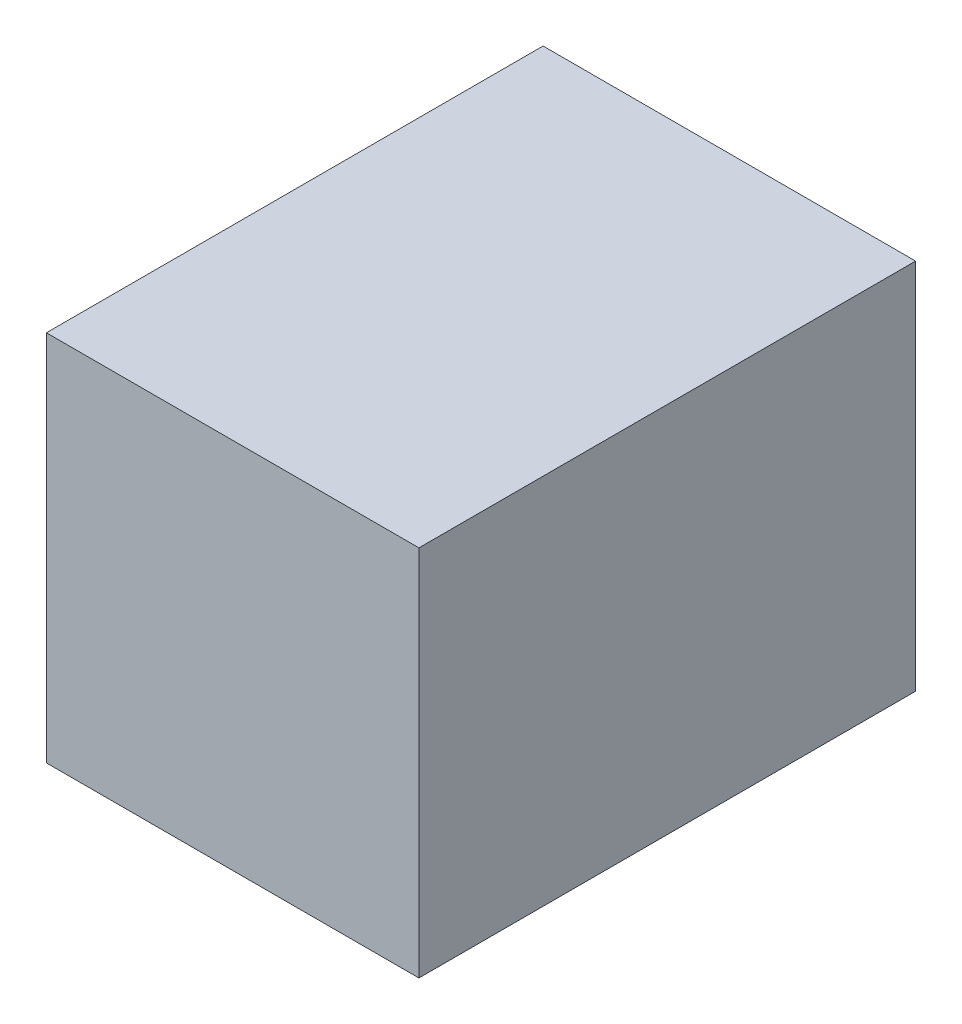
SolidWorks part; units mm, degrees
material "Plain Carbon Steel"
ref_plane "Front Plane" through (0, 0, 0) normal (0, 0, 1) x (1, 0, 0)
ref_plane "Top Plane" through (0, 0, 0) normal (0, 1, 0) x (1, 0, 0)
ref_plane "Right Plane" through (0, 0, 0) normal (1, 0, 0) x (0, 0, -1)
sketch "Sketch1" plane through (0, 0, 0) normal (0, 0, 1) x (1, 0, 0)
  line L1 (0, 0) -> (9.525, 0)
  line L2 (0, 0) -> (0, 9.525)
  line L3 (0, 9.525) -> (9.525, 9.525)
  line L4 (9.525, 0) -> (9.525, 9.525)
  dimension "D1" = 9.525
  dimension "D2" = 9.525
extrude "Boss-Extrude1" add sketch "Sketch1" along normal blind 12.7
